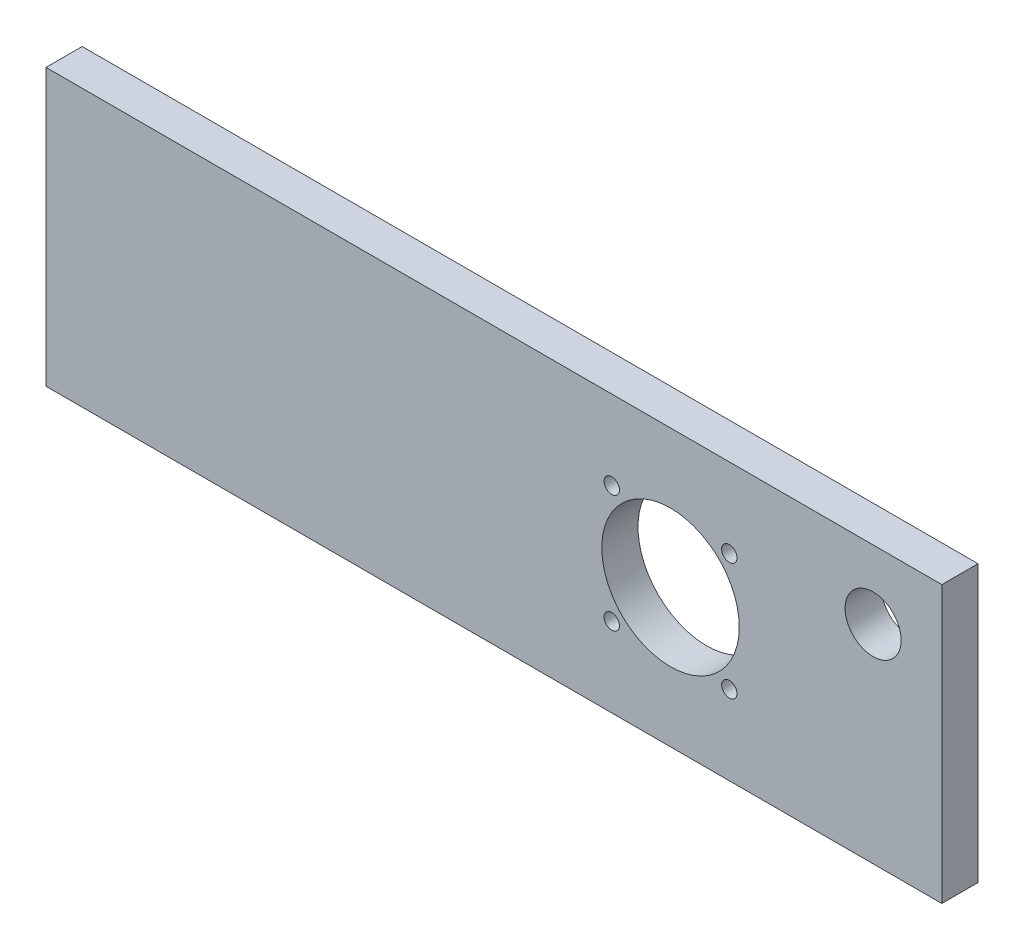
SolidWorks part; units mm, degrees
ref_plane "Front" through (0, 0, 0) normal (0, 0, 1) x (1, 0, 0)
ref_plane "Top" through (0, 0, 0) normal (0, 1, 0) x (1, 0, 0)
ref_plane "Right" through (0, 0, 0) normal (1, 0, 0) x (0, 0, -1)
sketch "Sketch1" plane through (0, 0, 0) normal (0, 0, 1) x (1, 0, 0)
  line L0 (172.65, 0) -> (172.65, 38.1762) construction
  line L1 (0, 0) -> (247.65, 0)
  line L2 (0, 0) -> (0, 76.3524)
  line L3 (0, 76.3524) -> (247.65, 76.3524)
  line L4 (247.65, 0) -> (247.65, 76.3524)
  line L5 (188.9, 21.9262) -> (156.4, 21.9262) construction
  line L6 (188.9, 21.9262) -> (188.9, 54.4262) construction
  line L7 (188.9, 54.4262) -> (156.4, 54.4262) construction
  line L8 (156.4, 21.9262) -> (156.4, 54.4262) construction
  line L9 (188.9, 21.9262) -> (156.4, 54.4262) construction
  line L10 (188.9, 54.4262) -> (156.4, 21.9262) construction
  line L11 (172.65, 38.1762) -> (172.65, 76.3524) construction
  line L12 (228.65, 76.3524) -> (228.65, 57.3524) construction
  line L13 (228.65, 57.3524) -> (247.65, 57.3524) construction
  circle A0 centre (172.65, 38.1762) radius 19
  circle A1 centre (156.4, 54.4262) radius 2.125
  circle A2 centre (188.9, 54.4262) radius 2.125
  circle A3 centre (188.9, 21.9262) radius 2.125
  circle A4 centre (156.4, 21.9262) radius 2.125
  circle A5 centre (228.65, 57.3524) radius 7.75
  dimension "D3" = 38
  dimension "D4" = 4.25
  dimension "D5" = 75
  dimension "D6" = 32.5
  dimension "D7" = 15.5
  dimension "D8" = 19
  dimension "D1" = 76.3524
  dimension "D2" = 247.65
extrude "Boss-Extrude1" add sketch "Sketch1" along normal blind 10 contours L1 L4 L3 L2
